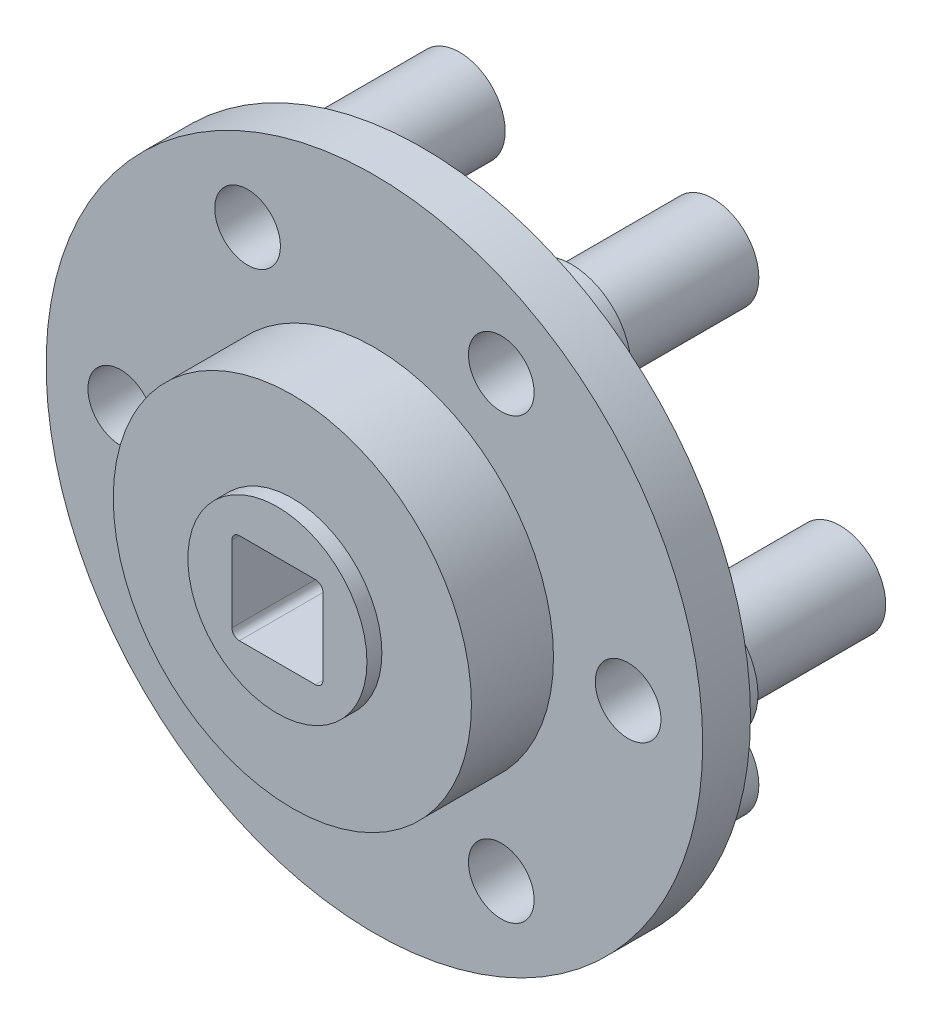
SolidWorks part; units mm, degrees
ref_plane "前视基准面" through (0, 0, 0) normal (0, 0, 1) x (1, 0, 0)
ref_plane "上视基准面" through (0, 0, 0) normal (0, 1, 0) x (1, 0, 0)
ref_plane "右视基准面" through (0, 0, 0) normal (1, 0, 0) x (0, 0, -1)
sketch "草图1" plane through (0, 0, 0) normal (0, 1, 0) x (1, 0, 0)
  line L0 (22, 11) -> (0, 11)
  line L1 (0, 11) -> (0, 10)
  line L2 (0, 10) -> (22, 10)
  line L3 (22, 10) -> (22, 11)
  line L4 (0, 11) -> (0, 10) construction
revolve "旋转1" add sketch "草图1" angle 360 about L4
sketch "草图2" plane through (0, 0, -10) normal (0, 0, 1) x (1, 0, 0)
  circle A0 centre (0, 0) radius 22
extrude "凸台-拉伸1" add sketch "草图2" along normal blind 10
ref_plane "基准面4" through (0, -14.7224, 0) normal (0, 1, 0) x (1, 0, 0)
sketch "草图3" plane through (0, -14.7224, 0) normal (0, 1, 0) x (1, 0, 0)
  line L0 (11.56, 22) -> (8.5, 22)
  line L1 (8.5, 22) -> (8.5, 11)
  line L2 (8.5, 11) -> (12.5, 11)
  line L3 (12.5, 11) -> (12.5, 12.5)
  line L4 (12.5, 12.5) -> (11.56, 12.5)
  line L5 (11.56, 12.5) -> (11.56, 22)
  line L6 (8.5, 22) -> (8.5, 11) construction
revolve "旋转2" add sketch "草图3" angle 360 about L6
sketch "草图4" plane through (0, -14.7224, 0) normal (0, 1, 0) x (1, 0, 0)
  line L0 (-5.44, 22) -> (-8.5, 22)
  line L1 (-8.5, 22) -> (-8.5, 11)
  line L2 (-8.5, 11) -> (-4.5, 11)
  line L3 (-4.5, 11) -> (-4.5, 12.5)
  line L4 (-4.5, 12.5) -> (-5.44, 12.5)
  line L5 (-5.44, 12.5) -> (-5.44, 22)
  line L6 (-8.5, 22) -> (-8.5, 11) construction
revolve "旋转3" add sketch "草图4" angle 360 about L6
sketch "草图5" plane through (0, 0, 0) normal (0, 1, 0) x (1, 0, 0)
  line L0 (-13.94, 22) -> (-17, 22)
  line L1 (-17, 22) -> (-17, 11)
  line L2 (-17, 11) -> (-13, 11)
  line L3 (-13, 11) -> (-13, 12.5)
  line L4 (-13, 12.5) -> (-13.94, 12.5)
  line L5 (-13.94, 12.5) -> (-13.94, 22)
  line L6 (-17, 22) -> (-17, 11) construction
revolve "旋转4" add sketch "草图5" angle 360 about L6
ref_plane "基准面5" through (0, 14.7224, 0) normal (0, 1, 0) x (1, 0, 0)
sketch "草图6" plane through (0, 14.7224, 0) normal (0, 1, 0) x (1, 0, 0)
  line L0 (-5.44, 22) -> (-8.5, 22)
  line L1 (-8.5, 22) -> (-8.5, 11)
  line L2 (-8.5, 11) -> (-4.5, 11)
  line L3 (-4.5, 11) -> (-4.5, 12.5)
  line L4 (-4.5, 12.5) -> (-5.44, 12.5)
  line L5 (-5.44, 12.5) -> (-5.44, 22)
  line L6 (-8.5, 22) -> (-8.5, 11) construction
revolve "旋转5" add sketch "草图6" angle 360 about L6
sketch "草图7" plane through (0, 14.7224, 0) normal (0, 1, 0) x (1, 0, 0)
  line L0 (11.56, 22) -> (8.5, 22)
  line L1 (8.5, 22) -> (8.5, 11)
  line L2 (8.5, 11) -> (12.5, 11)
  line L3 (12.5, 11) -> (12.5, 12.5)
  line L4 (12.5, 12.5) -> (11.56, 12.5)
  line L5 (11.56, 12.5) -> (11.56, 22)
  line L6 (8.5, 22) -> (8.5, 11) construction
revolve "旋转6" add sketch "草图7" angle 360 about L6
sketch "草图8" plane through (0, 0, 0) normal (0, 1, 0) x (1, 0, 0)
  line L0 (20.06, 22) -> (17, 22)
  line L1 (17, 22) -> (17, 11)
  line L2 (17, 11) -> (21, 11)
  line L3 (21, 11) -> (21, 12.5)
  line L4 (21, 12.5) -> (20.06, 12.5)
  line L5 (20.06, 12.5) -> (20.06, 22)
  line L6 (17, 22) -> (17, 11) construction
revolve "旋转7" add sketch "草图8" angle 360 about L6
hole_wizard "M3 六角头机械螺钉的柱形沉头孔1" positions "草图10" profile "草图9" counterbore size "M3" standard "ANSI Metric"
sketch "草图10" plane through (0, 0, -11) normal (0, 0, -1) x (-1, 0, 0)
  point P0 (15.5885, 9)
  point P1 (0, 18)
  point P2 (-15.5885, 9)
  point P3 (-15.5885, -9)
  point P4 (0, -18)
  point P5 (15.5885, -9)
sketch "草图9" plane through (-15.5885, 9, -11) normal (1, 0, 0) x (0, 1, 0)
  line L0 (0, 0) -> (0, 11)
  line L1 (0, 11) -> (1.7, 11)
  line L3 (1.7, 11) -> (1.7, 6)
  line L4 (1.7, 6) -> (2.25, 6)
  line L5 (2.25, 6) -> (2.25, 0)
  line L7 (2.25, 0) -> (0, 0)
  line L11 (0, -6.35) -> (0, 107.95) construction
  dimension "通孔孔直径" = 3.4
  dimension "通孔孔深度" = 11
  dimension "柱形沉头孔直径" = 4.5
  dimension "柱形沉头孔深度" = 6
hole_wizard "孔1" positions "草图12" profile "草图11" legacy
sketch "草图12" plane through (0, 0, -11) normal (0, 0, -1) x (-1, 0, 0)
  point P0 (0, 0)
sketch "草图11" plane through (0, 0, -11) normal (1, 0, 0) x (0, 1, 0)
  line L0 (0, 0) -> (0, 5)
  line L1 (0, 5) -> (4, 5)
  line L2 (4, 5) -> (4, 3)
  line L3 (4, 3) -> (5.08, 3)
  line L4 (5.08, 3) -> (5.08, 0)
  line L5 (5.08, 0) -> (0, 0)
  line L6 (0, 110) -> (0, -10) construction
  dimension "直径" = 8
  dimension "深度" = 5
  dimension "柱坑直径" = 10.16
  dimension "柱坑深度" = 3
hole_wizard "M3 六角头机械螺钉的柱形沉头孔2" positions "草图14" profile "草图13" counterbore size "M3" standard "ANSI Metric"
sketch "草图14" plane through (0, 0, 0) normal (0, 0, 1) x (1, 0, 0)
  point P0 (8.5, -14.7224)
  point P1 (-8.5, -14.7224)
  point P2 (-17, 0)
  point P3 (-8.5, 14.7224)
  point P4 (8.5, 14.7224)
  point P5 (17, 0)
sketch "草图13" plane through (8.5, -14.7224, 0) normal (1, 0, 0) x (0, -1, 0)
  line L0 (0, 0) -> (0, 22)
  line L1 (0, 22) -> (1.7, 22)
  line L3 (1.7, 22) -> (1.7, 3)
  line L4 (1.7, 3) -> (3.05, 3)
  line L5 (3.05, 3) -> (3.05, 0)
  line L7 (3.05, 0) -> (0, 0)
  line L11 (0, -6.35) -> (0, 107.95) construction
  dimension "通孔孔直径" = 3.4
  dimension "通孔孔深度" = 22
  dimension "柱形沉头孔直径" = 6.1
  dimension "柱形沉头孔深度" = 3
sketch "草图16" plane through (0, 0, 0) normal (0, 0, 1) x (1, 0, 0)
  circle A0 centre (-15.5885, 9) radius 2.4
  circle A1 centre (0, 18) radius 2.4
  circle A2 centre (15.5885, 9) radius 2.4
  circle A3 centre (15.5885, -9) radius 2.4
  circle A4 centre (0, -18) radius 2.4
  circle A5 centre (-15.5885, -9) radius 2.4
extrude "凸台-拉伸2" add sketch "草图16" against normal blind 11
sketch "草图17" plane through (0, 0, 0) normal (0, 0, 1) x (1, 0, 0)
  circle A0 centre (0, 0) radius 22
extrude "切除-拉伸2" cut sketch "草图17" against normal blind 7.8
sketch "草图18" plane through (0, 0, -7.8) normal (0, 0, 1) x (1, 0, 0)
  circle A0 centre (0, 0) radius 12
extrude "凸台-拉伸3" add sketch "草图18" along normal blind 5.5
sketch "草图19" plane through (0, 0, -2.3) normal (0, 0, 1) x (1, 0, 0)
  circle A0 centre (0, 0) radius 6
extrude "凸台-拉伸4" add sketch "草图19" along normal blind 1
sketch "草图20" plane through (0, 0, -1.3) normal (0, 0, 1) x (1, 0, 0)
  line L9 (-2.55, 3.05) -> (2.55, 3.05)
  line L10 (-3.05, 2.55) -> (-3.05, -2.55)
  line L11 (-2.55, -3.05) -> (2.55, -3.05)
  line L12 (3.05, 2.55) -> (3.05, -2.55)
  line L13 (-3.05, 3.05) -> (3.05, -3.05) construction
  line L14 (-3.05, -3.05) -> (3.05, 3.05) construction
  arc A8 (-2.55, 3.05) -> (-3.05, 2.55) centre (-2.55, 2.55) ccw
  arc A9 (2.55, 3.05) -> (3.05, 2.55) centre (2.55, 2.55) cw
  arc A10 (3.05, -2.55) -> (2.55, -3.05) centre (2.55, -2.55) cw
  arc A11 (-2.55, -3.05) -> (-3.05, -2.55) centre (-2.55, -2.55) cw
  point P0 (0, 0)
  point P1 (0, 0)
  point P2 (0, 0)
  dimension "D1" = 0.5
extrude "切除-拉伸3" cut sketch "草图20" against normal blind 6
sketch "草图21" plane through (0, 0, -7.8) normal (0, 0, 1) x (1, 0, 0)
  circle A0 centre (-8.5, -14.7224) radius 2.2
  circle A1 centre (-17, 0) radius 2.2
  circle A2 centre (-8.5, 14.7224) radius 2.2
  circle A3 centre (8.5, 14.7224) radius 2.2
  circle A4 centre (17, 0) radius 2.2
  circle A5 centre (8.5, -14.7224) radius 2.2
extrude "切除-拉伸4" cut sketch "草图21" against normal blind 3.5
